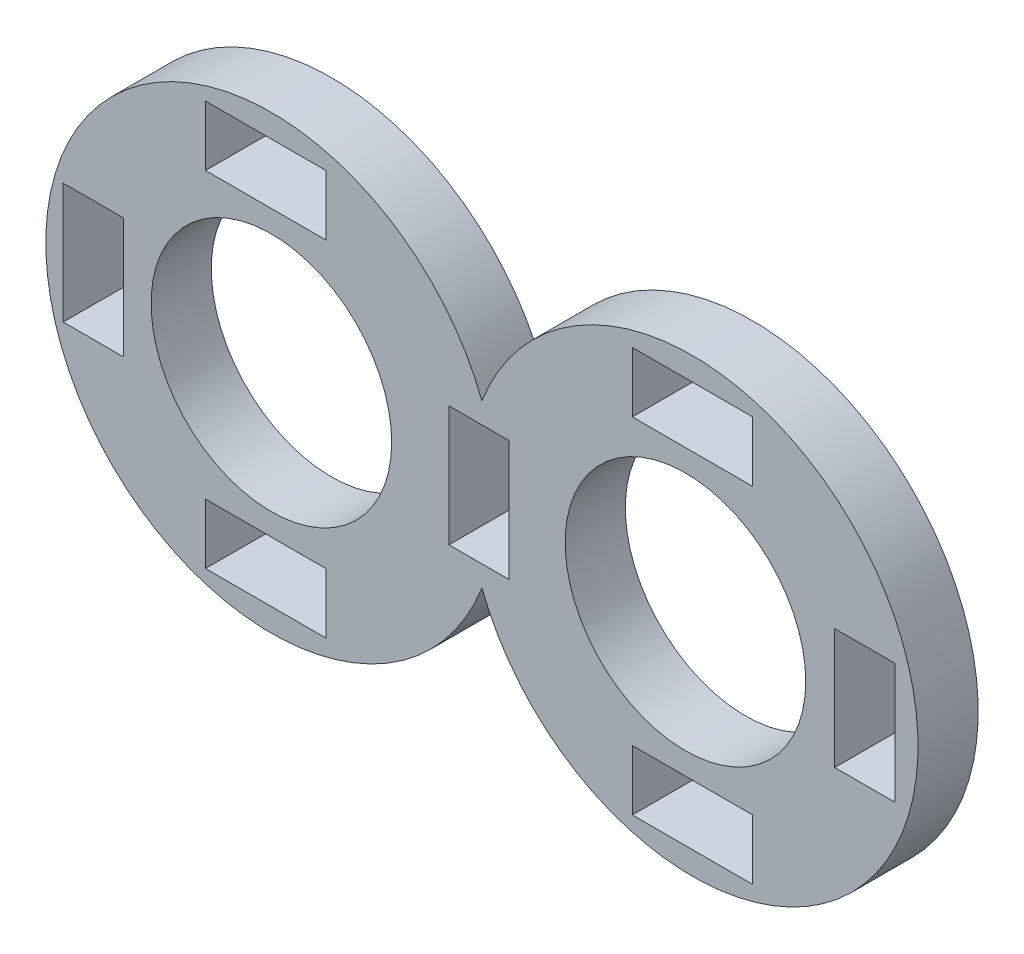
SolidWorks part; units mm, degrees
ref_plane "Front Plane" through (0, 0, 0) normal (0, 0, 1) x (1, 0, 0)
ref_plane "Top Plane" through (0, 0, 0) normal (0, 1, 0) x (1, 0, 0)
ref_plane "Right Plane" through (0, 0, 0) normal (1, 0, 0) x (0, 0, -1)
sketch "Sketch1" plane through (0, 0, 0) normal (0, 0, 1) x (1, 0, 0)
  line L0 (7, 0) -> (0, 0) construction
  circle A0 centre (0, 0) radius 3.75
  circle A1 centre (7, 0) radius 3.75
  circle A2 centre (0, 0) radius 2
  circle A3 centre (7, 0) radius 2
extrude "Boss-Extrude1" add sketch "Sketch1" along normal blind 1 contours A0 | A1
sketch "Sketch2" plane through (0, 0, 0) normal (0, 0, 1) x (1, 0, 0)
  circle A0 centre (0, 0) radius 2
  circle A1 centre (6.8835, 0) radius 2
extrude "Cut-Extrude3" cut sketch "Sketch2" along normal blind 1 from surface at 0 starting at face at (3.5, 0, 0)
sketch "Sketch3" plane through (0, 0, 0) normal (0, 0, 1) x (1, 0, 0)
  line L5 (6, -2.3653) -> (8, -2.3653)
  line L6 (9.3653, -1) -> (10.3653, -1)
  line L7 (9.3653, -1) -> (9.3653, 1)
  line L8 (9.3653, 1) -> (10.3653, 1)
  line L9 (10.3653, -1) -> (10.3653, 1)
  line L12 (6, -2.3653) -> (6, -3.3653)
  line L13 (6, -3.3653) -> (8, -3.3653)
  line L14 (8, -2.3653) -> (8, -3.3653)
  line L15 (8, 2.3653) -> (6, 2.3653)
  line L16 (8, 2.3653) -> (8, 3.3653)
  line L17 (8, 3.3653) -> (6, 3.3653)
  line L18 (6, 2.3653) -> (6, 3.3653)
  line L20 (0.9046, -2.3653) -> (0.9046, -3.3653)
  line L21 (0.9046, -3.3653) -> (-1.0954, -3.3653)
  line L22 (-1.0954, -2.3653) -> (-1.0954, -3.3653)
  line L23 (0.9046, -2.3653) -> (-1.0954, -2.3653)
  line L24 (0.9046, 2.3653) -> (0.9046, 3.3653)
  line L25 (-1.0954, 3.3653) -> (0.9046, 3.3653)
  line L26 (-1.0954, 2.3653) -> (-1.0954, 3.3653)
  line L27 (-1.0954, 2.3653) -> (0.9046, 2.3653)
  line L28 (-2.4607, -1) -> (-3.4607, -1)
  line L29 (-2.4607, -1) -> (-2.4607, 1)
  line L30 (-2.4607, 1) -> (-3.4607, 1)
  line L31 (-3.4607, -1) -> (-3.4607, 1)
  line L33 (3.9523, -1) -> (2.9523, -1)
  line L34 (3.9523, -1) -> (3.9523, 1)
  line L35 (3.9523, 1) -> (2.9523, 1)
  line L36 (2.9523, -1) -> (2.9523, 1)
  dimension "D3" = 2
  dimension "D4" = 2
extrude "Cut-Extrude4" cut sketch "Sketch3" along normal blind 1 from surface at 0 starting at face at (2, 0, 0)
